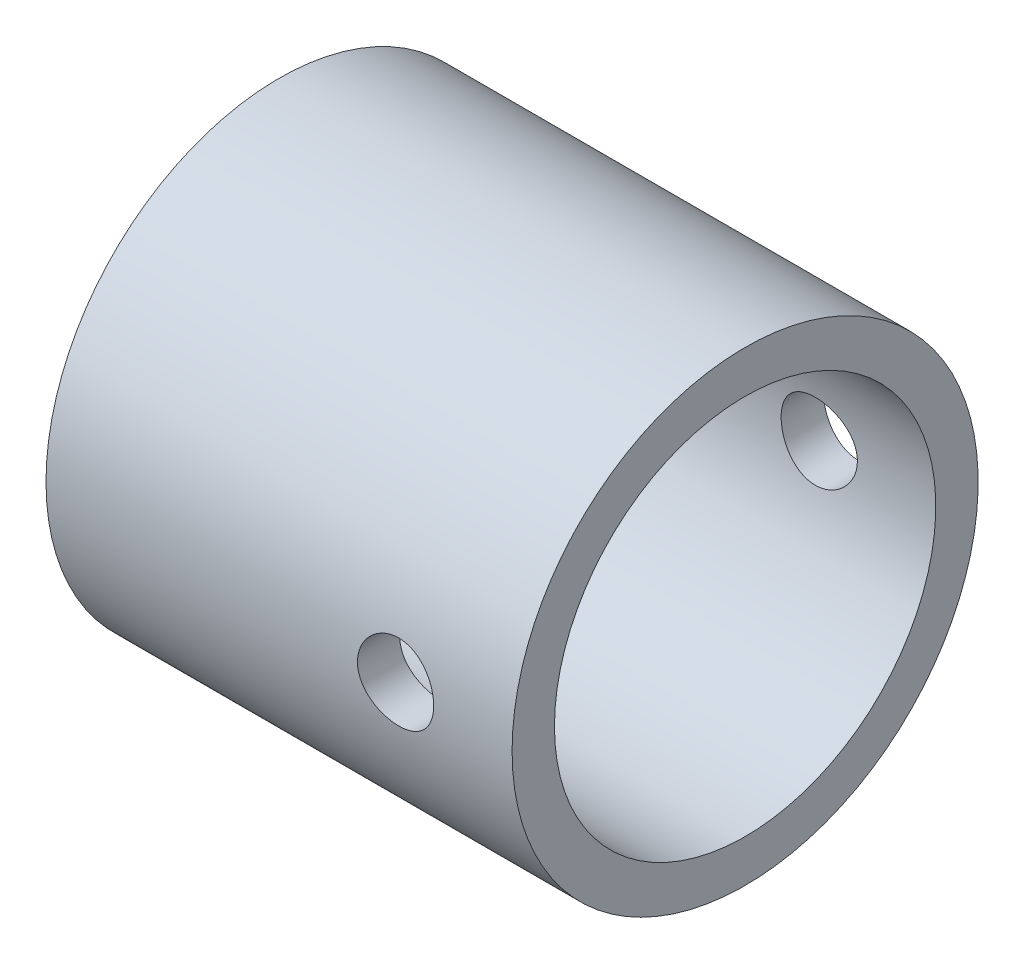
SolidWorks part; units mm, degrees
ref_plane "Front Plane" through (0, 0, 0) normal (0, 0, 1) x (1, 0, 0)
ref_plane "Top Plane" through (0, 0, 0) normal (0, 1, 0) x (1, 0, 0)
ref_plane "Right Plane" through (0, 0, 0) normal (1, 0, 0) x (0, 0, -1)
sketch "Sketch3" plane through (0, 0, 0) normal (0, 0, 1) x (1, 0, 0)
  line L0 (-58.5481, 189.9573) -> (284.033, 189.9573) construction
  line L2 (213.4012, -189.6279) -> (558.7345, -189.6279) construction
  line L4 (263.0584, -148.5737) -> (308.4812, -148.5737) construction
  line L42 (262.5584, -144.0737) -> (272.5584, -144.0737)
  line L43 (272.5584, -144.0737) -> (272.5584, -143.0737)
  line L45 (261.5584, -143.0737) -> (272.5584, -143.0737)
  line L55 (261.5584, -144.3237) -> (261.5584, -148.0737)
  line L63 (263.0584, -148.0737) -> (263.0584, -144.5737)
  line L64 (263.0584, -148.0737) -> (261.5584, -148.0737)
  line L65 (263.0584, -144.5737) -> (262.5584, -144.5737)
  line L66 (262.5584, -144.5737) -> (262.5584, -144.0737)
  line L97 (261.5584, -144.3237) -> (261.5584, -143.0737)
  dimension "D2" = 1.5
  dimension "D3" = 1
  dimension "D4" = 1
  dimension "D5" = 4
  dimension "D6" = 4.5
  dimension "D7" = 10
  dimension "D10" = 11
revolve "Revolve19" add sketch "Sketch3" angle 360 about L4
sketch "Sketch5" plane through (0, 0, 0) normal (0, 0, 1) x (1, 0, 0)
  line L0 (272.5584, -143.0737) -> (272.5584, -154.0737) construction
  line L1 (261.5584, -148.5737) -> (272.5584, -148.5737) construction
  line L2 (261.5584, -143.0737) -> (261.5584, -154.0737) construction
  line L3 (267.0584, -143.0737) -> (267.0584, -154.0737) construction
  line L4 (272.5584, -143.0737) -> (261.5584, -143.0737) construction
  line L5 (261.5584, -154.0737) -> (272.5584, -154.0737) construction
  line L6 (269.8084, -143.0737) -> (269.8084, -154.0737) construction
  circle A0 centre (269.8084, -148.5737) radius 0.9
  point P18 (0, 0)
  dimension "D2" = 1.8
  dimension "D1" = 2.75
extrude "Cut-Extrude2" cut sketch "Sketch5" against normal through all and the other way through all
